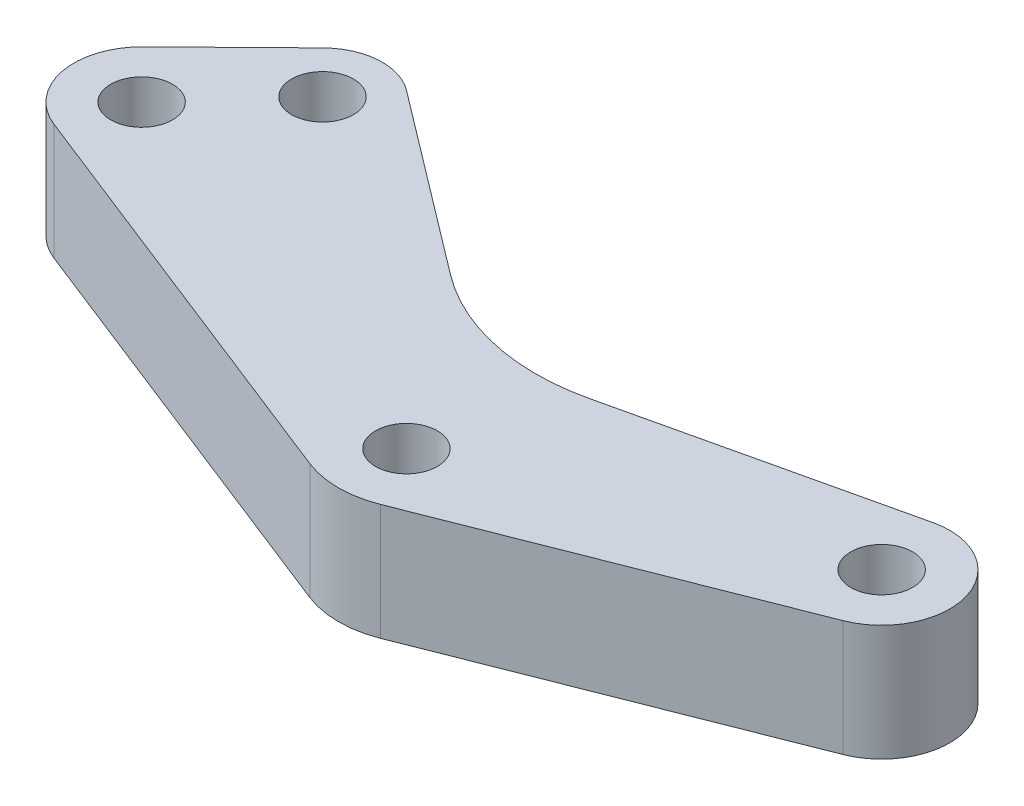
SolidWorks part; units mm, degrees
material "MDF"
ref_plane "Plano frontal" through (0, 0, 0) normal (0, 0, 1) x (1, 0, 0)
ref_plane "Plano superior" through (0, 0, 0) normal (0, 1, 0) x (1, 0, 0)
ref_plane "Plano direito" through (0, 0, 0) normal (1, 0, 0) x (0, 0, -1)
ref_plane "Plano1" through (0, -6, 0) normal (0, -1, 0) x (1, 0, 0)
sketch "Esboço1" plane through (0, -6, 0) normal (0, -1, 0) x (1, 0, 0)
  line L0 (23.6582, -5.4198) -> (1.8308, 3.1692)
  line L1 (-1.8308, 3.1692) -> (-23.6582, -5.4198)
  line L2 (-24.8257, -11.1771) -> (-20.1015, -15.8044)
  line L3 (-16.06, -16.0604) -> (-6.6439, -8.9246)
  line L4 (6.6439, -8.9246) -> (16.06, -16.0604)
  line L5 (20.1015, -15.8044) -> (24.8257, -11.1771)
  line L6 (0, 0) -> (-22.3767, -8.6767) construction
  line L7 (0, 0) -> (22.3767, -8.6767) construction
  line L8 (-22.3767, -8.6767) -> (22.3767, -8.6767) construction
  line L9 (-17.9323, -13.5898) -> (17.9323, -13.5898) construction
  line L10 (17.9323, -13.5898) -> (0, 0) construction
  line L11 (0, 0) -> (-17.9323, -13.5898) construction
  arc A0 (1.8308, 3.1692) -> (-1.8308, 3.1692) centre (0, -1.4835) ccw
  arc A1 (-23.6582, -5.4198) -> (-24.8257, -11.1771) centre (-22.3767, -8.6767) ccw
  arc A2 (-20.1015, -15.8044) -> (-16.06, -16.0604) centre (-17.9323, -13.5898) ccw
  arc A3 (-6.6439, -8.9246) -> (6.6439, -8.9246) centre (0, -17.6915) cw
  arc A4 (16.06, -16.0604) -> (20.1015, -15.8044) centre (17.9323, -13.5898) ccw
  arc A5 (24.8257, -11.1771) -> (23.6582, -5.4198) centre (22.3767, -8.6767) ccw
  circle A6 centre (-17.9323, -13.5898) radius 1.6
  circle A7 centre (0, 0) radius 1.6
  circle A8 centre (17.9323, -13.5898) radius 1.6
  circle A9 centre (-22.3767, -8.6767) radius 1.6
  circle A10 centre (22.3767, -8.6767) radius 1.6
  point P24 (0, -13.5898)
  point P25 (0, -8.6767)
  dimension "D1" = 3.2
  dimension "D2" = 24
  dimension "D4" = 3.5
  dimension "D9" = 11
  dimension "D12" = 3.5
  dimension "D13" = 3.6195
  dimension "D15" = 5
  dimension "D3" = 3.6195
  dimension "D5" = 137.612
  dimension "D6" = 105.688
  dimension "D7" = 22.5
  dimension "D8" = 3.1
  dimension "D11" = 17.6915
  dimension "D14" = 3.1
extrude "Ressalto-extrusão1" add sketch "Esboço1" against normal blind 6
sketch "Esboço5" plane through (0, -6, 0) normal (0, -1, 0) x (1, 0, 0)
  circle A0 centre (17.9323, -13.5898) radius 1.6 construction
  circle A1 centre (22.3767, -8.6767) radius 1.6 construction
  circle A2 centre (17.9323, -13.5898) radius 1.6
  circle A3 centre (22.3767, -8.6767) radius 1.6
extrude "Ressalto-extrusão2" add sketch "Esboço5" against normal up to surface (6 mm away) up to face at (22.3767, 0, -7.0767)
sketch "Esboço2" plane through (0, -6, 0) normal (0, -1, 0) x (1, 0, 0)
  line L0 (2.4707, -6.9726) -> (16.9231, -10.3039)
  line L1 (23.6582, -5.4198) -> (1.8308, 3.1692) construction
  line L2 (0, 0) -> (22.3767, -8.6767) construction
  line L3 (20.1015, -15.8044) -> (24.8257, -11.1771) construction
  line L4 (6.6439, -8.9246) -> (16.06, -16.0604) construction
  line L5 (23.6582, -5.4198) -> (1.8308, 3.1692)
  line L6 (20.1015, -15.8044) -> (24.8257, -11.1771)
  line L7 (6.6439, -8.9246) -> (16.06, -16.0604)
  arc A0 (6.6439, -8.9246) -> (-6.6439, -8.9246) centre (0, -17.6915) ccw construction
  arc A1 (16.9231, -10.3039) -> (19.0056, -3.589) centre (17.7149, -6.8691) ccw
  circle A2 centre (17.7149, -6.8691) radius 1.6
  arc A4 (24.8257, -11.1771) -> (23.6582, -5.4198) centre (22.3767, -8.6767) ccw construction
  arc A6 (16.06, -16.0604) -> (20.1015, -15.8044) centre (17.9323, -13.5898) ccw construction
  arc A7 (24.8257, -11.1771) -> (23.6582, -5.4198) centre (22.3767, -8.6767) ccw
  arc A8 (16.06, -16.0604) -> (20.1015, -15.8044) centre (17.9323, -13.5898) ccw
  arc A9 (6.6439, -8.9246) -> (-6.6439, -8.9246) centre (0, -17.6915) ccw
  circle A10 centre (0, 0) radius 1.6 construction
  point P16 (0, 0)
  point P17 (0, 0)
  point P18 (0, 0)
  point P19 (1.9688, -6.8691)
  point P20 (0, 0)
  dimension "D1" = 19
extrude "Corte-extrusão1" cut sketch "Esboço2" against normal blind 10 and the other way through all
